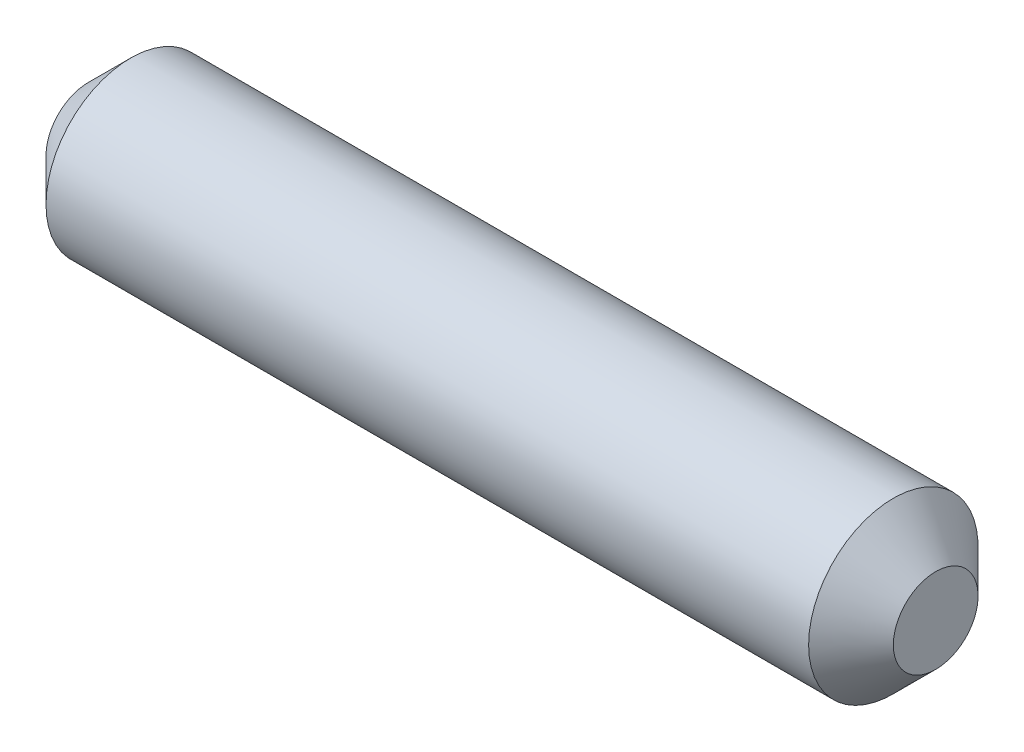
SolidWorks part; units mm, degrees
ref_plane "Plan de face" through (0, 0, 0) normal (0, 0, 1) x (1, 0, 0)
ref_plane "Plan de dessus" through (0, 0, 0) normal (0, 1, 0) x (1, 0, 0)
ref_plane "Plan de droite" through (0, 0, 0) normal (1, 0, 0) x (0, 0, -1)
sketch "Esquisse1" plane through (0, 0, 0) normal (0, 0, 1) x (1, 0, 0)
  line L0 (-64.5455, 0) -> (114.6852, 0) construction
  line L1 (0, 0) -> (0, 1)
  line L2 (0, 1) -> (1, 2)
  line L3 (1, 2) -> (19, 2)
  line L4 (19, 2) -> (20, 1)
  line L5 (20, 1) -> (20, 0)
  line L6 (20, 0) -> (0, 0)
  dimension "D1" = 1
  dimension "D2" = 1
  dimension "D3" = 1
  dimension "D4" = 1
  dimension "D5" = 20
  dimension "D6" = 4
revolve "Révolution1" add sketch "Esquisse1" angle 360 about L0
